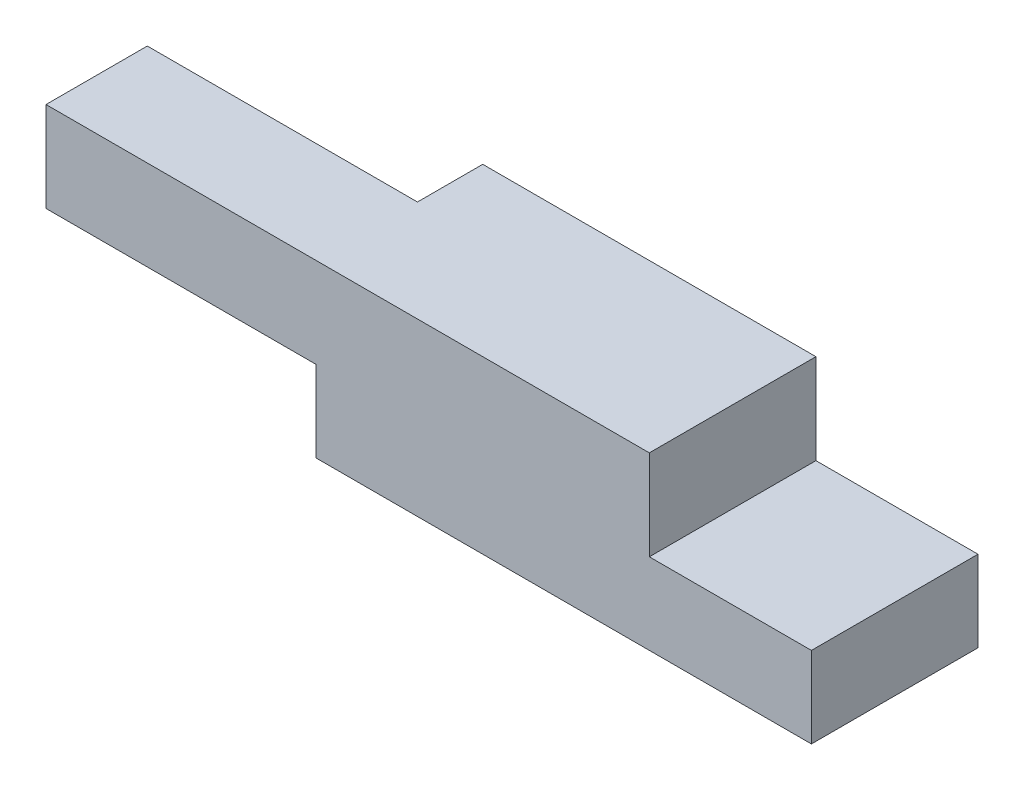
SolidWorks part; units mm, degrees
ref_plane "Front Plane" through (0, 0, 0) normal (0, 0, 1) x (1, 0, 0)
ref_plane "Top Plane" through (0, 0, 0) normal (0, 1, 0) x (1, 0, 0)
ref_plane "Right Plane" through (0, 0, 0) normal (1, 0, 0) x (0, 0, -1)
sketch "Sketch1" plane through (0, 0, 0) normal (0, 1, 0) x (1, 0, 0)
  line L1 (-27.5, 9.25) -> (27.5, 9.25)
  line L2 (-27.5, 9.25) -> (-27.5, -9.25)
  line L3 (-27.5, -9.25) -> (27.5, -9.25)
  line L4 (27.5, 9.25) -> (27.5, -9.25)
  line L5 (-27.5, 9.25) -> (27.5, -9.25) construction
  line L6 (-27.5, -9.25) -> (27.5, 9.25) construction
  point P0 (0, 0)
  dimension "D1" = 18.5
  dimension "D2" = 55
extrude "Boss-Extrude1" add sketch "Sketch1" along normal blind 9
sketch "Sketch2" plane through (0, 9, 0) normal (0, 1, 0) x (1, 0, 0)
  line L0 (-27.5, -9.25) -> (27.5, -9.25) construction
  line L1 (-27.5, 9.25) -> (9.5, 9.25)
  line L2 (-27.5, 9.25) -> (-27.5, -9.25)
  line L3 (-27.5, -9.25) -> (9.5, -9.25)
  line L4 (9.5, 9.25) -> (9.5, -9.25)
  dimension "D1" = 37
extrude "Boss-Extrude2" add sketch "Sketch2" along normal blind 10
sketch "Sketch3" plane through (-27.5, 0, 0) normal (-1, 0, 0) x (0, 0, 1)
  line L0 (0, 0) -> (0, 19) construction
  line L1 (-9.25, 0) -> (9.25, 0) construction
  line L2 (-9.25, 19) -> (9.25, 19) construction
  line L4 (-2, 0) -> (2, 0)
  line L5 (-2, 0) -> (-2, 19)
  line L6 (-2, 19) -> (2, 19)
  line L7 (2, 0) -> (2, 19)
  line L8 (-2, 0) -> (2, 19) construction
  line L9 (-2, 19) -> (2, 0) construction
  point P6 (0, 9.5)
  dimension "D1" = 4
extrude "Boss-Extrude3" add sketch "Sketch3" along normal blind 4
sketch "Sketch4" plane through (-27.5, 0, 0) normal (-1, 0, 0) x (0, 0, 1)
  line L0 (-2, 19) -> (-2, 0) construction
  line L1 (9.25, 19) -> (-2, 19)
  line L2 (9.25, 19) -> (9.25, 9)
  line L3 (9.25, 9) -> (-2, 9)
  line L4 (-2, 19) -> (-2, 9)
  dimension "D1" = 10
extrude "Boss-Extrude4" add sketch "Sketch4" along normal blind 30
